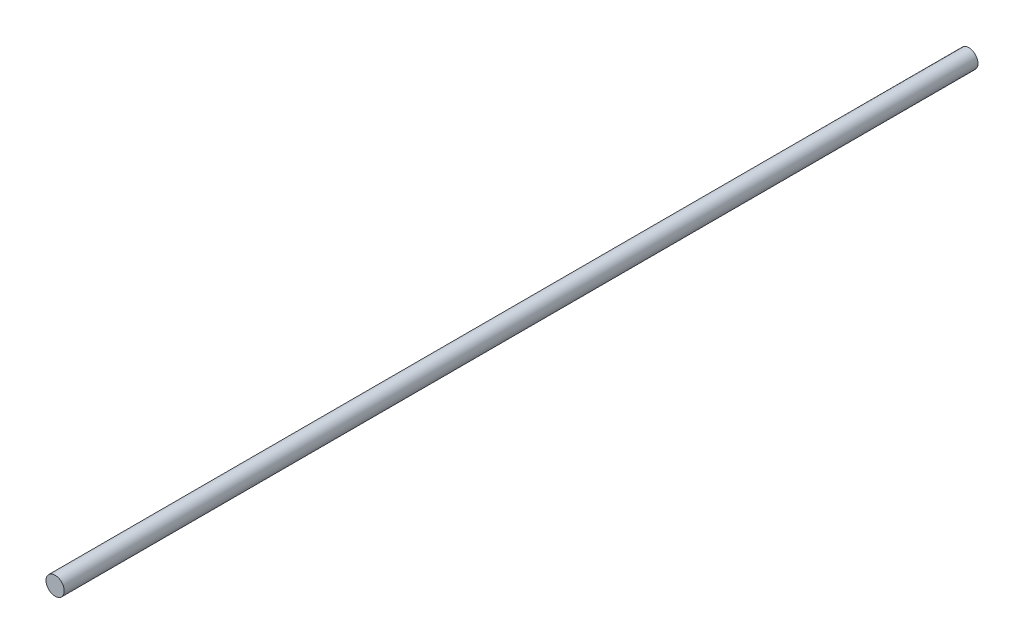
SolidWorks part; units mm, degrees
ref_plane "Plan de face" through (0, 0, 0) normal (0, 0, 1) x (1, 0, 0)
ref_plane "Plan de dessus" through (0, 0, 0) normal (0, 1, 0) x (1, 0, 0)
ref_plane "Plan de droite" through (0, 0, 0) normal (1, 0, 0) x (0, 0, -1)
sketch "Esquisse1" plane through (0, 0, 0) normal (0, 0, 1) x (1, 0, 0)
  circle A0 centre (0, 0) radius 4
  dimension "D1" = 8
extrude "Boss.-Extru.1" add sketch "Esquisse1" along normal blind 400
